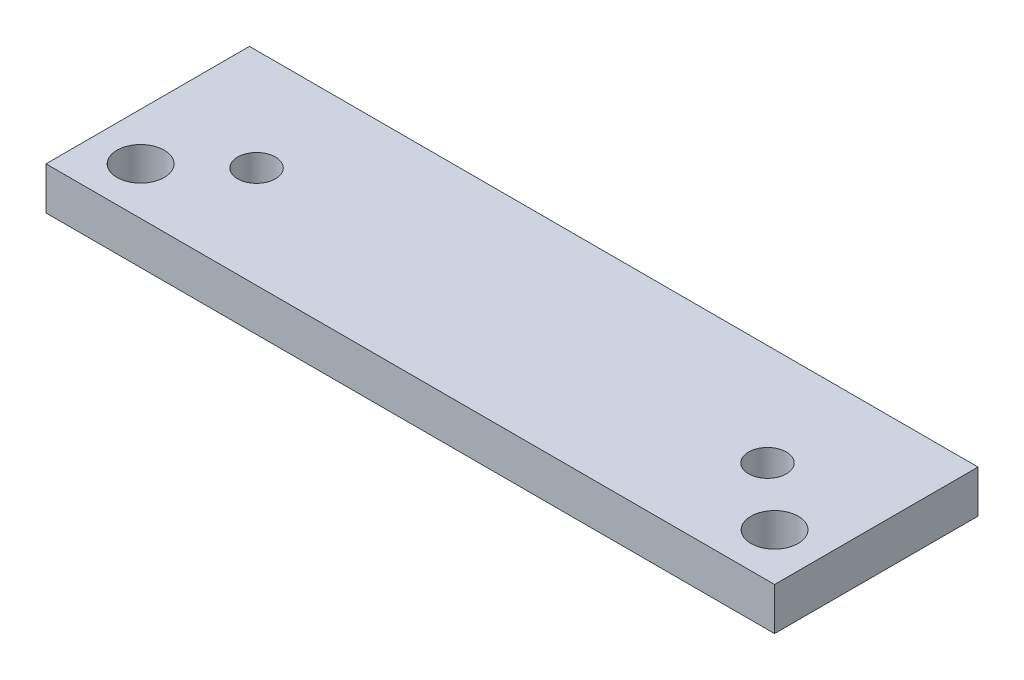
SolidWorks part; units mm, degrees
ref_plane "前视基准面" through (0, 0, 0) normal (0, 0, 1) x (1, 0, 0)
ref_plane "上视基准面" through (0, 0, 0) normal (0, 1, 0) x (1, 0, 0)
ref_plane "右视基准面" through (0, 0, 0) normal (1, 0, 0) x (0, 0, -1)
other "Configuration Table"
sketch "草图1" plane through (0, 0, 0) normal (0, 1, 0) x (1, 0, 0)
  line L0 (0, 10.75) -> (77, 10.75) construction
  line L1 (0, 0) -> (77, 0)
  line L2 (0, 0) -> (0, 21.5)
  line L3 (0, 21.5) -> (77, 21.5)
  line L4 (77, 0) -> (77, 21.5)
  line L5 (38.5, 21.5) -> (38.5, 45.3598) construction
  circle A0 centre (11.5, 10.75) radius 2
  circle A1 centre (65.5, 10.75) radius 2
  circle A2 centre (5, 5) radius 2.5
  circle A3 centre (72, 5) radius 2.5
  point P17 (0, 6.8492)
  dimension "D3" = 27
  dimension "D4" = 4
  dimension "D5" = 5
  dimension "D1" = 21.5
  dimension "D2" = 77
  dimension "D6" = 5
  dimension "D7" = 5
extrude "凸台-拉伸1" add sketch "草图1" along normal blind 4.5
